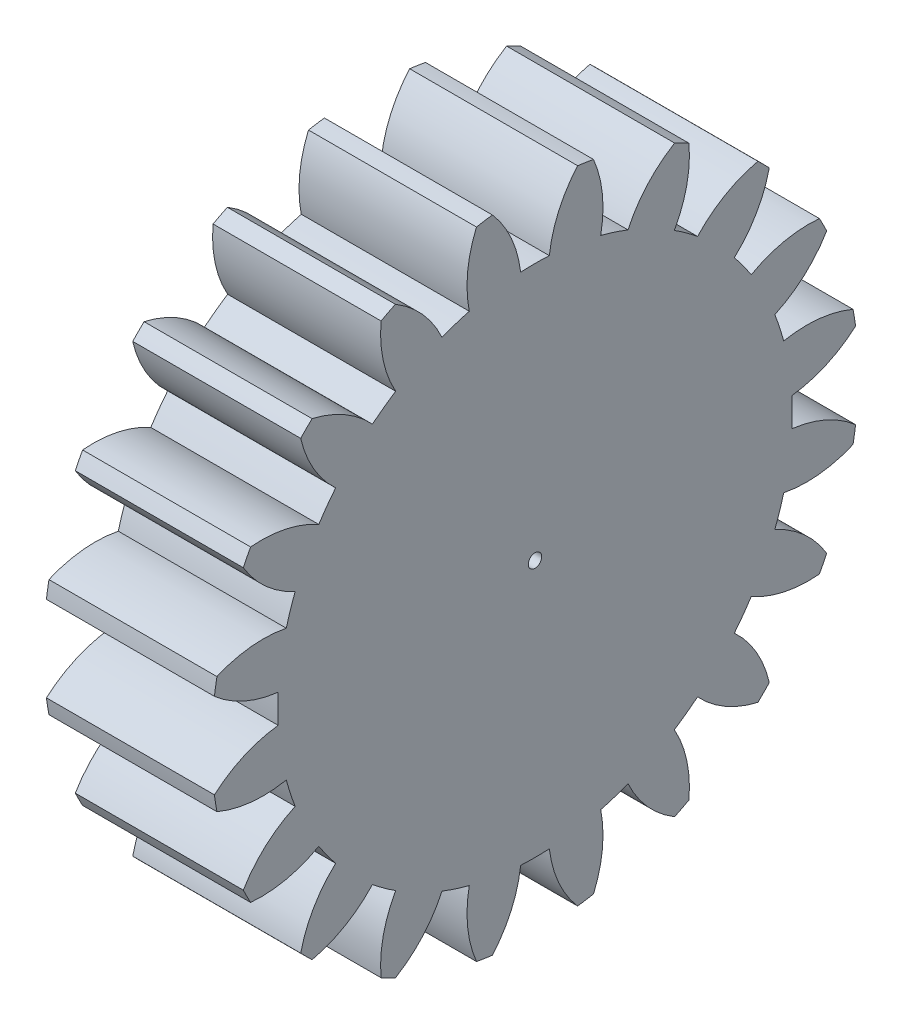
SolidWorks part; units mm, degrees
ref_plane "Plane1" through (0, 0, 0) normal (0, 0, 1) x (1, 0, 0)
ref_plane "Plane2" through (0, 0, 0) normal (0, 1, 0) x (1, 0, 0)
ref_plane "Plane3" through (0, 0, 0) normal (1, 0, 0) x (0, 0, -1)
other "Configuration Table"
sketch "HoldingSke" plane through (0, 0, 0) normal (0, 1, 0) x (1, 0, 0)
  line L0 (0, 0) -> (0.537, -0.1954)
  line L1 (-15, 0) -> (100, 0) construction
  line L2 (0, 0) -> (-2.1039, 2.3779)
  line L3 (0, 0) -> (-11.863, 4.5341)
  line L4 (0, 0) -> (8.1152, 2.9537)
  line L5 (0, 0) -> (-46.8476, -17.4728)
  line L6 (0, 0) -> (-8.2896, -5.593)
  line L7 (-2.1039, 2.3779) -> (8.6586, 51.2059)
  line L8 (-76.2, 54.61) -> (-76.1, 54.61)
  line L9 (-71.009, 38.7566) -> (-53.1078, 45.2721)
  line L10 (-76.2, 71.12) -> (104.1128, 71.12)
  line L11 (0, 0) -> (-10, 0)
  line L12 (-76.2, 101.6) -> (-76.147, 101.6)
  line L13 (24.9733, 27.94) -> (52.9518, 28.4284)
  line L14 (24.9733, 27.94) -> (24.9743, 27.94)
  line L15 (24.9733, 27.94) -> (100.4006, 29.5858)
  line L16 (-63.627, -1.75) -> (-12.827, -1.75)
  circle A0 centre (0, 0) radius 0.4
  circle A1 centre (0, 0) radius 15.3115
  circle A2 centre (0, 0) radius 37.5
  circle A3 centre (0, 0) radius 0.4
  dimension "MHD" = 30.623
  dimension "Hub_dia" = 75
  dimension "Bore" = 0.8
  dimension "MBD" = 0.8
  dimension "Num_teeth" = 20
  dimension "Pitch" = 0.5714
  dimension "Overall_len" = 50
  dimension "Show_teeth" = 20
  dimension "Thickness" = 10
  dimension "OAL" = 50.0001
  dimension "T_dim" = 0.1
  dimension "Ap" = 20
  dimension "H" = 19.05
  dimension "Pitch_radius" = 180.3128
  dimension "Width" = 10
  dimension "Backlash" = 0.053
  dimension "Addendum_fac" = 1
  dimension "Dedendum_fac" = 1.25
  dimension "Clearance_fac" = 0.25
  dimension "Dedendum_add" = 0.001
  dimension "Module" = 1.75
sketch "BasProSke" plane through (0, 0, 0) normal (0, 1, 0) x (1, 0, 0)
  line L0 (-10, 0) -> (60, 0) construction
  line L1 (0, 0) -> (0, 19.25)
  line L2 (0, 0) -> (10, 0)
  line L3 (10, 0) -> (10, 19.25)
  line L4 (10, 19.25) -> (0, 19.25)
  dimension "Thickness" = 10
  dimension "Diameter" = 38.5
revolve "Base-Revolve" add sketch "BasProSke" angle 360 about L0
sketch "TooCutSke" plane through (0, 0, 0) normal (1, 0, 0) x (0, 0, -1)
  line L1 (0, 0) -> (0, 107) construction
  line L2 (0, 0) -> (-1.4657, 17.4385) construction
  line L3 (0, 0) -> (-5.4605, 34.4765) construction
  line L4 (-1.4657, 17.4385) -> (-2.7303, 17.2382) construction
  arc A0 (0.8543, 15.2877) -> (-0.8543, 15.2877) centre (0, 0) ccw
  arc A1 (2.558, 19.1049) -> (-2.558, 19.1049) centre (0, 0) ccw
  circle A2 centre (0, 0) radius 17.5 construction
  circle A3 centre (0, 0) radius 16.4446 construction
  arc A4 (-0.8543, 15.2877) -> (-2.558, 19.1049) centre (-7.8067, 14.4734) ccw
  arc A5 (2.558, 19.1049) -> (0.8543, 15.2877) centre (7.8067, 14.4734) ccw
  dimension "Root_dia" = 30.623
  dimension "Overcut_dia" = 38.5508
  dimension "Pitch_dia" = 35
  dimension "Base_dia" = 32.8892
  dimension "Flank_rad" = 7
  dimension "Half_ang" = 9
  dimension "Half_CT" = 1.2803
extrude "ToothCut" cut sketch "TooCutSke" along normal through all
fillet "Breaks" [suppressed] radius 0.035
fillet "RootFillets" [suppressed] radius 0.4385
pattern_circular "TeethCuts" count 20 every 18 about axis through (-10, 0, 0) along (1, 0, 0) of "ToothCut", "RootFillets", "Breaks"
sketch "HubNeaOneSke" plane through (0, 0, 0) normal (-1, 0, 0) x (0, 0, 1)
  circle A0 centre (0, 0) radius 15.3115
  dimension "Diameter" = 30.623
extrude "HubNearOne" [suppressed] add sketch "HubNeaOneSke" along normal blind 40.0001
sketch "HubNeaBotSke" plane through (0, 0, 0) normal (-1, 0, 0) x (0, 0, 1)
  circle A0 centre (0, 0) radius 15.3115
  dimension "Diameter" = 30.623
extrude "HubNearBoth" [suppressed] add sketch "HubNeaBotSke" along normal blind 20
ref_plane "FarPln" through (10, 0, 0) normal (1, 0, 0) x (0, 0, -1)
sketch "HubFarSke" plane through (10, 0, 0) normal (1, 0, 0) x (0, 0, -1)
  circle A0 centre (0, 0) radius 15.3115
  dimension "Diameter" = 30.623
extrude "HubFar" [suppressed] add sketch "HubFarSke" along normal blind 20
sketch "BorSke" plane through (0, 0, 0) normal (1, 0, 0) x (0, 0, -1)
  circle A0 centre (0, 0) radius 0.4
  dimension "Diameter" = 0.8
extrude "Bore" cut sketch "BorSke" along normal mid plane 100.0001
sketch "KeySke" plane through (0, 0, 0) normal (1, 0, 0) x (0, 0, -1)
  line L0 (-0.05, 0) -> (-0.05, 0.5)
  line L1 (-0.05, 0.5) -> (0.05, 0.5)
  line L2 (0.05, 0.5) -> (0.05, 0)
  line L3 (0, 0) -> (0, 34) construction
  line L4 (-0.05, 0) -> (0.05, 0)
  dimension "Offset" = 0.5
  dimension "Width" = 0.1
extrude "Keyway" [suppressed] cut sketch "KeySke" along normal mid plane 100.0001
pattern_circular "Keyway2" [suppressed] count 2 every 90 about axis through (-10, 0, 0) along (1, 0, 0)
equation "' \"Module@HoldingSke\" = 6.35"
equation "' \"Num_teeth@HoldingSke\" = 12"
equation "' \"Ap@HoldingSke\" =  20"
equation "' \"Ap@HoldingSke\" = 20"
equation "' \"Width@HoldingSke\" = 0.5 * 25.4"
equation "' \"Hub_dia@HoldingSke\"= 1 * 25.4"
equation "' \"Hub_dia@HoldingSke\" = 1 * 25.4"
equation "' \"Overall_len@HoldingSke\" = 1.0 * 25.4"
equation "' \"Bore@HoldingSke\" = 0.75 * 25.4"
equation "' \"T_dim@HoldingSke\" = 0.1 * 25.4"
equation "' \"Width@KeySke\" = 0.25 * 25.4"
equation "' \"Show_teeth@HoldingSke\" = 13"
equation "' \"Backlash@HoldingSke\" = 0.009 * 25.4"
equation "' \"Addendum_fac@HoldingSke\" = 1.0"
equation "' \"Dedendum_fac@HoldingSke\" = 1.25"
equation "' \"Dedendum_add@HoldingSke\" = 0.00005 * 25.4"
equation "' \"Clearance_fac@HoldingSke\" = 0.25"
equation "\"Pitch@HoldingSke\" = 1 / \"Module@HoldingSke\""
equation "\"Overcut_dia@TooCutSke\" = (\"Num_teeth@HoldingSke\" + 2 * \"Addendum_fac@HoldingSke\") / \"Pitch@HoldingSke\" + 0.002 * 25.4"
equation "\"Pitch_dia@TooCutSke\" = \"Num_teeth@HoldingSke\" / \"Pitch@HoldingSke\""
equation "\"Base_dia@TooCutSke\" = \"Num_teeth@HoldingSke\" / \"Pitch@HoldingSke\" * cos((\"Ap@HoldingSke\"  * 3.14159265 / 180))"
equation "\"Root_dia@TooCutSke\" = (\"Num_teeth@HoldingSke\" + 2) / \"Pitch@HoldingSke\" - 2 * (\"Addendum_fac@HoldingSke\" + \"Dedendum_fac@HoldingSke\") / \"Pitch@HoldingSke\" - \"Dedendum_add@HoldingSke\" * 2"
equation "\"Half_ang@TooCutSke\" = 180 / \"Num_teeth@HoldingSke\""
equation "\"Half_CT@TooCutSke\" = \"Num_teeth@HoldingSke\" / \"Pitch@HoldingSke\" * sin((3.14159265 / 2 / \"Num_teeth@HoldingSke\")) / 2 - 7 * \"Backlash@HoldingSke\" / 4"
equation "\"Flank_rad@TooCutSke\" = \"Num_teeth@HoldingSke\" / \"Pitch@HoldingSke\" / 5"
equation "\"Radius@RootFillets\" = \"Clearance_fac@HoldingSke\" / \"Pitch@HoldingSke\" + \"Dedendum_add@HoldingSke\""
equation "\"Break_rad@Breaks\" = 0.02 / \"Pitch@HoldingSke\""
equation "\"Thickness@HoldingSke\" = \"Width@HoldingSke\""
equation "\"OAL@HoldingSke\" = \"Thickness@HoldingSke\""
equation "\"MHD@HoldingSke\" = (\"Num_teeth@HoldingSke\" + 2) / \"Pitch@HoldingSke\" - 2 * (\"Addendum_fac@HoldingSke\" + \"Dedendum_fac@HoldingSke\")  / \"Pitch@HoldingSke\" - \"Dedendum_add@HoldingSke\" * 2"
equation "\"MBD@HoldingSke\" = (\"Num_teeth@HoldingSke\" + 2) / \"Pitch@HoldingSke\" - 2 * (\"Addendum_fac@HoldingSke\" + \"Dedendum_fac@HoldingSke\")  / \"Pitch@HoldingSke\" - \"Dedendum_add@HoldingSke\" * 2 - 0.002 * 25.4"
equation "\"MHD@HoldingSke\" = ((sgn( \"MHD@HoldingSke\" - \"Hub_dia@HoldingSke\" )-1)*( \"MHD@HoldingSke\" - \"Hub_dia@HoldingSke\" ))/-2+ \"Hub_dia@HoldingSke\""
equation "\"MBD@HoldingSke\" = ((sgn( \"MBD@HoldingSke\" - \"Bore@HoldingSke\" )-1)*( \"MBD@HoldingSke\" - \"Bore@HoldingSke\" ))/-2+ \"Bore@HoldingSke\""
equation "\"OAL@HoldingSke\" = ((sgn( \"OAL@HoldingSke\" - \"Overall_len@HoldingSke\" )+1)*( \"OAL@HoldingSke\" - \"Overall_len@HoldingSke\" ))/2 + \"Overall_len@HoldingSke\" + 0.000002 * 25.4"
equation "\"Num_teeth@TeethCuts\" = int( \"Show_teeth@HoldingSke\" ) + 1"
equation "\"Num_teeth@TeethCuts\" = ((sgn( \"Num_teeth@TeethCuts\" - \"Num_teeth@HoldingSke\" )-1)*( \"Num_teeth@TeethCuts\" - \"Num_teeth@HoldingSke\" ))/-2+ \"Num_teeth@HoldingSke\""
equation "\"Num_teeth@TeethCuts\" = ((sgn( \"Num_teeth@TeethCuts\" - 2.0)+1)*( \"Num_teeth@TeethCuts\" - 2.0))/2 +2.0"
equation "\"Angle@TeethCuts\" = 360.0 / \"Num_teeth@HoldingSke\""
equation "\"Diameter@BasProSke\" = (\"Num_teeth@HoldingSke\" + 2 * \"Addendum_fac@HoldingSke\") / \"Pitch@HoldingSke\""
equation "\"Thickness@BasProSke\"  = \"Thickness@HoldingSke\""
equation "' \"Fillet_rad@BasProSke\" =  \"Thickness@HoldingSke\" * 0.05"
equation "' \"Fillet_rad@BasProSke\" = \"Thickness@HoldingSke\" * 0.05"
equation "\"MHD@HoldingSke\" = ((sgn( \"MHD@HoldingSke\" - \"Root_dia@TooCutSke\" )-1)*( \"MHD@HoldingSke\" - \"Root_dia@TooCutSke\" ))/-2+ \"Root_dia@TooCutSke\""
equation "\"Diameter@HubNeaOneSke\" = \"MHD@HoldingSke\""
equation "\"Length@HubNearOne\" = \"OAL@HoldingSke\" - \"Thickness@BasProSke\""
equation "\"Diameter@HubNeaBotSke\" = \"MHD@HoldingSke\""
equation "\"Length@HubNearBoth\" = ( \"OAL@HoldingSke\" - \"Thickness@BasProSke\" ) / 2.0"
equation "\"Thickness@FarPln\" = \"Thickness@BasProSke\""
equation "\"Diameter@HubFarSke\" = \"MHD@HoldingSke\""
equation "\"Length@HubFar\" = ( \"OAL@HoldingSke\" - \"Thickness@BasProSke\" ) / 2.0"
equation "\"Diameter@BorSke\" = \"MBD@HoldingSke\""
equation "\"D1@Bore\" = \"OAL@HoldingSke\" * 2.0"
equation "\"D1@Keyway\" = \"OAL@HoldingSke\" * 2.0"
equation "\"Offset@KeySke\" = \"T_dim@HoldingSke\" + \"MBD@HoldingSke\" / 2.0"
